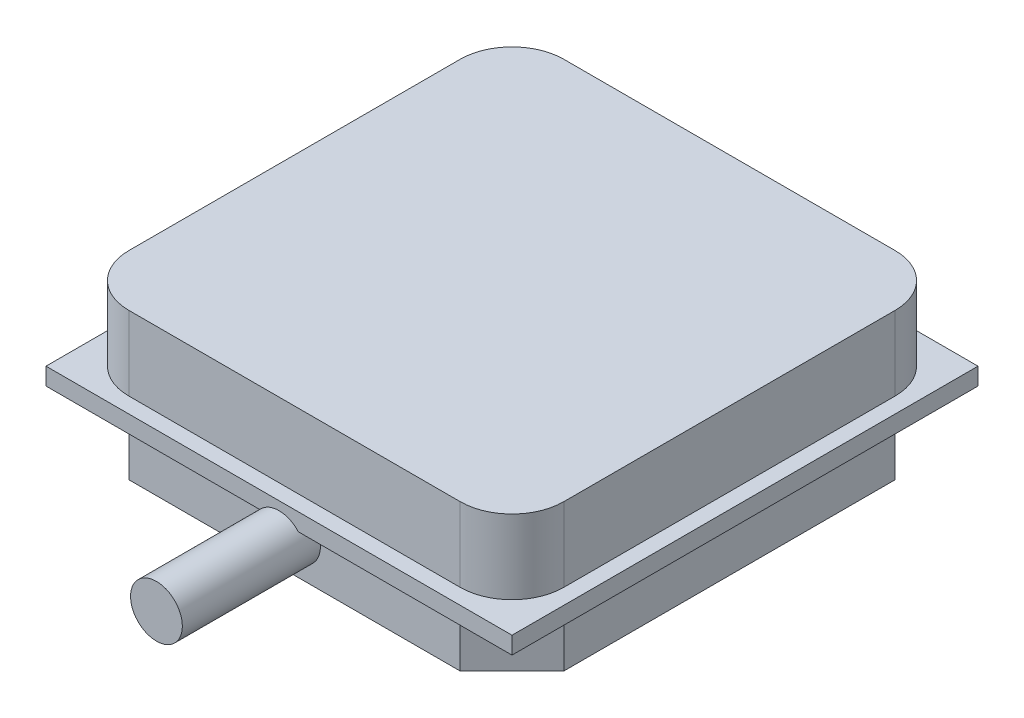
SolidWorks part; units mm, degrees
ref_plane "Front Plane" through (0, 0, 0) normal (0, 0, 1) x (1, 0, 0)
ref_plane "Top Plane" through (0, 0, 0) normal (0, 1, 0) x (1, 0, 0)
ref_plane "Right Plane" through (0, 0, 0) normal (1, 0, 0) x (0, 0, -1)
sketch "Sketch1" plane through (0, 0, 0) normal (0, 1, 0) x (1, 0, 0)
  line L1 (0, 0) -> (27, 0)
  line L2 (0, 0) -> (0, 27)
  line L3 (0, 27) -> (27, 27)
  line L4 (27, 0) -> (27, 27)
  dimension "D1" = 27
  dimension "D2" = 27
extrude "Boss-Extrude1" add sketch "Sketch1" along normal blind 1
sketch "Sketch2" plane through (0, 1, 0) normal (0, 1, 0) x (1, 0, 0)
  line L0 (0, 0) -> (27, 0) construction
  line L1 (3.9, 26.1) -> (23.1, 26.1)
  line L2 (0.9, 23.1) -> (0.9, 3.9)
  line L3 (3.9, 0.9) -> (23.1, 0.9)
  line L4 (26.1, 23.1) -> (26.1, 3.9)
  line L5 (0, 27) -> (0, 0) construction
  arc A0 (0.9, 3.9) -> (3.9, 0.9) centre (3.9, 3.9) ccw
  arc A1 (23.1, 0.9) -> (26.1, 3.9) centre (23.1, 3.9) ccw
  arc A2 (23.1, 26.1) -> (26.1, 23.1) centre (23.1, 23.1) cw
  arc A3 (3.9, 26.1) -> (0.9, 23.1) centre (3.9, 23.1) ccw
  point P10 (0.9, 0.9)
  point P13 (26.1, 0.9)
  point P18 (0.9, 26.1)
  dimension "D5" = 3
  dimension "D1" = 25.2
  dimension "D2" = 25.2
  dimension "D3" = 0.9
  dimension "D4" = 0.9
extrude "Boss-Extrude2" add sketch "Sketch2" along normal blind 4.3
sketch "Sketch3" plane through (0, 0, 0) normal (0, -1, 0) x (1, 0, 0)
  line L0 (27, -27) -> (0, -27) construction
  line L1 (3.9, -0.9) -> (23.1, -0.9)
  line L2 (0.9, -3.9) -> (0.9, -23.1)
  line L3 (3.9, -26.1) -> (23.1, -26.1)
  line L4 (26.1, -3.9) -> (26.1, -23.1)
  line L5 (0, -27) -> (0, 0) construction
  line L6 (3.9, -0.9) -> (0.9, -3.9)
  line L7 (23.1, -0.9) -> (26.1, -3.9)
  line L8 (26.1, -23.1) -> (23.1, -26.1)
  line L9 (0.9, -23.1) -> (3.9, -26.1)
  point P0 (0.9, -0.9)
  point P1 (26.1, -26.1)
  point P2 (0.9, -26.1)
  point P3 (26.1, -0.9)
  dimension "D1" = 25.2
  dimension "D2" = 25.2
  dimension "D3" = 0.9
  dimension "D4" = 0.9
extrude "Boss-Extrude3" add sketch "Sketch3" along normal blind 3.2
sketch "Sketch4" plane through (0, 0, -0.9) normal (0, 0, 1) x (1, 0, 0)
  line L0 (23.1, 0) -> (3.9, 0) construction
  line L1 (0, 1) -> (0, 0) construction
  circle A0 centre (13.5, -1) radius 1.5
  dimension "D1" = 3
  dimension "D2" = 1
  dimension "D3" = 13.5
extrude "Boss-Extrude5" add sketch "Sketch4" along normal blind 8
